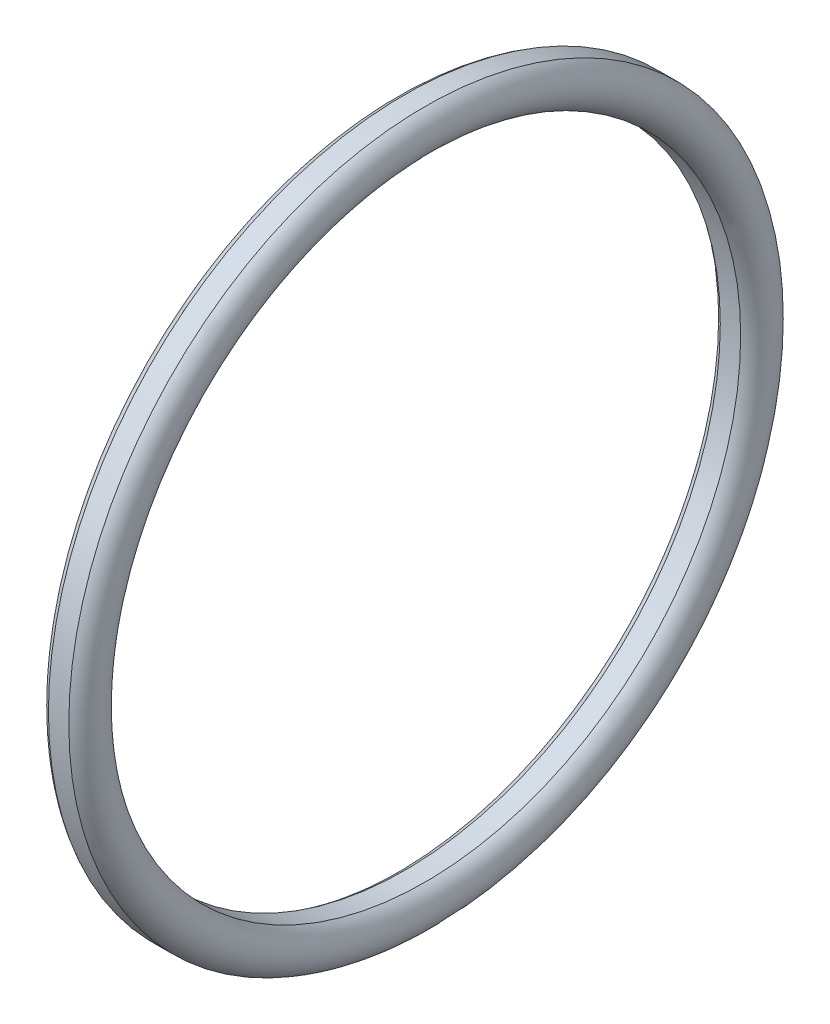
SolidWorks part; units mm, degrees
ref_plane "Front Plane" through (0, 0, 0) normal (0, 0, 1) x (1, 0, 0)
ref_plane "Top Plane" through (0, 0, 0) normal (0, 1, 0) x (1, 0, 0)
ref_plane "Right Plane" through (0, 0, 0) normal (1, 0, 0) x (0, 0, -1)
ref_axis "Axis1" through (88.99, 0, 0) along (-1, 0, 0)
sketch "Sketch1" plane through (0, 0, 0) normal (0, 0, 1) x (1, 0, 0)
  line L0 (0, 0) -> (1.2253, 0) construction
  line L1 (88.99, 0) -> (-88.99, 0) construction
  line L2 (0, 0) -> (0, 10) construction
  line L3 (0, 10) -> (1.2253, 10) construction
  line L4 (-0.2037, 10.4) -> (0.2037, 10.4) construction
  line L5 (-0.3161, 11.6253) -> (0.3161, 11.6253) construction
  line L6 (0, 11.5) -> (1.2253, 11.5) construction
  line L7 (1.2253, 11.5) -> (1.2253, 10) construction
  line L8 (0.3161, 11.6253) -> (0.4753, 11.6253) construction
  line L9 (0, 0) -> (1.2253, 0.858) construction
  line L10 (0, 0) -> (1.2253, -0.8265) construction
  line L11 (1.2253, 0) -> (1.2253, 0.858) construction
  line L12 (1.2253, 0) -> (1.2253, -0.8265) construction
  line L13 (0.4753, 11.6253) -> (1.2253, 11.5) construction
  line L14 (0.2037, 10.4) -> (0.4753, 10.4) construction
  line L15 (0.4753, 10.4) -> (1.2253, 10) construction
  line L16 (0.4753, 10.4) -> (0.4753, 11.6253) construction
  line L17 (1.2253, 10.75) -> (0.4753, 10.75) construction
  line L18 (0, 10.75) -> (0.75, 10.75) construction
  line L19 (-0.7479, 10.9475) -> (0.7479, 10.9475) construction
  line L20 (-0.3161, 11.6253) -> (0, 10.9475) construction
  line L21 (0, 10.9475) -> (0.3161, 11.6253) construction
  line L22 (0.2037, 10.4) -> (0, 11.1104) construction
  line L23 (0, 11.1104) -> (-0.2037, 10.4) construction
  line L24 (-0.739, 11.1104) -> (0.739, 11.1104) construction
  line L25 (0, 11.075) -> (-0.336, 11.75) construction
  line L26 (-2.7141, 11.75) -> (0, 11.75) construction
  line L27 (-2.7141, 11.75) -> (-2.7141, 10.4) construction
  line L28 (-2.7141, 10.4) -> (0, 10.4) construction
  line L29 (0, 11.75) -> (0, 10.4) construction
  line L30 (0.3955, 10.5821) -> (-0.3955, 10.9179) construction
  line L31 (-0.336, 11.75) -> (0.336, 11.75)
  line L32 (-0.336, 10.4) -> (0.336, 10.4)
  line L33 (0, 10.75) -> (1.1078, 10.9475) construction
  line L34 (-0.3955, 10.9179) -> (-0.3955, 10.5821)
  line L35 (0, 10.75) -> (-0.3955, 10.5821) construction
  line L36 (0.3955, 10.9179) -> (0.3955, 10.5821)
  circle A0 centre (0, 10.75) radius 0.75
  arc A1 (0.2037, 10.4) -> (-0.2037, 10.4) centre (0, 11.1104) ccw construction
  arc A2 (-0.3161, 11.6253) -> (0.3161, 11.6253) centre (0, 10.9475) ccw construction
  arc A3 (0.336, 10.4) -> (0.336, 11.75) centre (0, 11.075) ccw
  arc A4 (-0.336, 11.75) -> (-0.336, 10.4) centre (0, 11.075) ccw
  arc A5 (-0.3955, 10.5821) -> (0.3955, 10.5821) centre (0, 10.75) ccw
  arc A6 (0.3955, 10.9179) -> (-0.3955, 10.9179) centre (0, 10.75) ccw
  point P7 (0, 11.5)
  point P11 (0.739, 11.1104)
  point P19 (-0.739, 11.1104)
  point P29 (-0.7479, 10.9475)
  point P30 (0.7479, 10.9475)
  dimension "D1" = 1.5
  dimension "D7" = 50
  dimension "D9" = 26.463
  dimension "D4" = 34
  dimension "D6" = 61.928
  dimension "D8" = 32
  dimension "D10" = 46
  dimension "D12" = 0.754
  dimension "D15" = 0.739
  dimension "D2" = 20
  dimension "D3" = 35
  dimension "D5" = 99.486
  dimension "D11" = 23.5
  dimension "D13" = 20.8
  dimension "D14" = 1.35
sketch "Sketch2" plane through (0, 0, 0) normal (0, 0, 1) x (1, 0, 0)
  circle A0 centre (0, 10.75) radius 0.75
  circle A1 centre (0, 10.75) radius 0.75 construction
revolve "Revolve1" [suppressed] add sketch "Sketch2" angle 360 about axis through (88.99, 0, 0) along (-1, 0, 0)
sketch "Sketch3" plane through (0, 0, 0) normal (0, 0, 1) x (1, 0, 0)
  line L0 (0.2037, 10.4) -> (-0.2037, 10.4)
  arc A0 (0.2037, 10.4) -> (-0.2037, 10.4) centre (0, 11.1104) ccw
revolve "Revolve2" [suppressed] add sketch "Sketch3" angle 360 about axis through (88.99, 0, 0) along (-1, 0, 0)
sketch "Sketch4" plane through (0, 0, 0) normal (0, 0, 1) x (1, 0, 0)
  line L0 (0.3161, 11.6253) -> (-0.3161, 11.6253)
  arc A0 (-0.3161, 11.6253) -> (0.3161, 11.6253) centre (0, 10.9475) ccw
revolve "Revolve3" [suppressed] add sketch "Sketch4" angle 360 about axis through (88.99, 0, 0) along (-1, 0, 0)
sketch "Sketch5" plane through (0, 0, 0) normal (0, 0, 1) x (1, 0, 0)
  line L0 (-0.336, 11.75) -> (0.336, 11.75)
  line L1 (-0.336, 10.4) -> (0.336, 10.4)
  line L3 (-0.336, 11.75) -> (0.336, 11.75) construction
  arc A0 (-0.336, 11.75) -> (-0.336, 10.4) centre (0, 11.075) ccw
  arc A1 (0.336, 10.4) -> (0.336, 11.75) centre (0, 11.075) ccw
  arc A2 (0.336, 10.4) -> (0.336, 11.75) centre (0, 11.075) ccw construction
revolve "Revolve4" add sketch "Sketch5" angle 360 about axis through (88.99, 0, 0) along (-1, 0, 0)
sketch "Sketch6" plane through (0, 0, 0) normal (0, 0, 1) x (1, 0, 0)
  line L4 (0.3955, 10.5821) -> (0.3955, 10.9179)
  line L5 (-0.3955, 10.5821) -> (-0.3955, 10.9179)
  arc A0 (0.3955, 10.9179) -> (-0.3955, 10.9179) centre (0, 10.75) ccw
  arc A1 (-0.3955, 10.5821) -> (0.3955, 10.5821) centre (0, 10.75) ccw
revolve "Revolve5" [suppressed] add sketch "Sketch6" angle 360 about axis through (88.99, 0, 0) along (-1, 0, 0)
